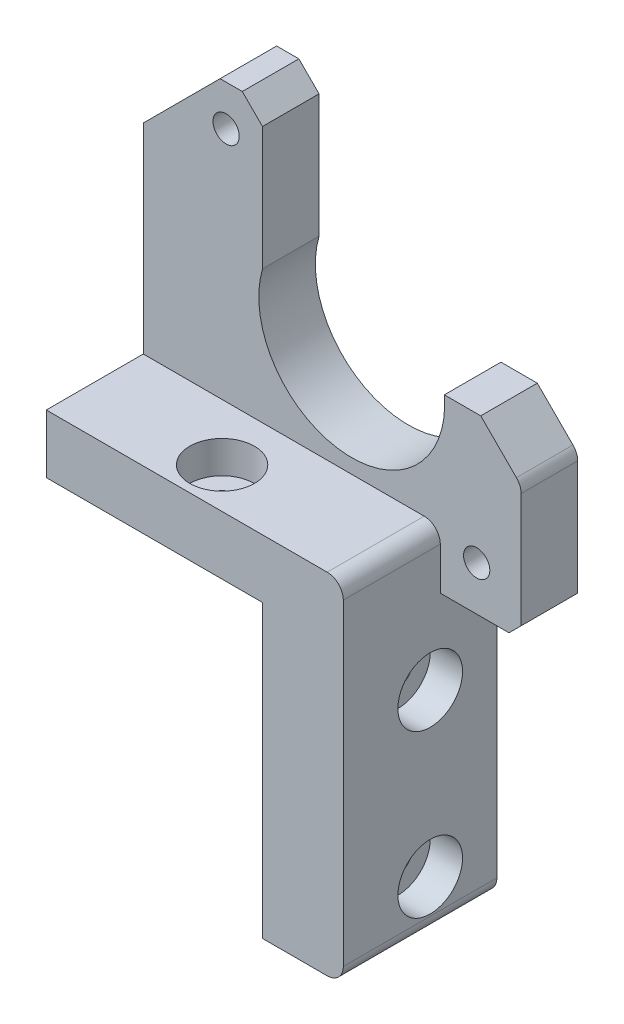
SolidWorks part; units mm, degrees
ref_plane "Front Plane" through (0, 0, 0) normal (0, 0, 1) x (1, 0, 0)
ref_plane "Top Plane" through (0, 0, 0) normal (0, 1, 0) x (1, 0, 0)
ref_plane "Right Plane" through (0, 0, 0) normal (1, 0, 0) x (0, 0, -1)
sketch "Sketch1" plane through (0, 0, 0) normal (0, 0, 1) x (1, 0, 0)
  line L0 (0, 0) -> (10, 0)
  line L1 (10, 0) -> (10, 43.25)
  line L2 (10, 43.25) -> (-26.75, 43.25)
  line L3 (-26.75, 43.25) -> (-26.75, 36)
  line L4 (-26.75, 36) -> (0, 36)
  line L5 (0, 36) -> (0, 0)
  dimension "D1" = 10
  dimension "D2" = 43.25
  dimension "D3" = 26.75
  dimension "D4" = 36
extrude "Boss-Extrude1" add sketch "Sketch1" along normal blind 19
sketch "Sketch2" plane through (0, 0, 0) normal (0, 0, -1) x (-1, 0, 0)
  line L0 (-10, 36) -> (26.75, 36)
  line L1 (26.75, 36) -> (26.75, 68)
  line L2 (26.75, 68) -> (17.25, 77.5)
  line L3 (17.25, 77.5) -> (14.5, 77.5)
  line L4 (14.5, 77.5) -> (12, 75)
  line L5 (12, 75) -> (12, 59.75)
  line L7 (-10, 0) -> (-10, 43.25) construction
  line L8 (-10, 36) -> (-18.5, 36)
  line L9 (-18.5, 36) -> (-20, 37.5)
  line L10 (-20, 37.5) -> (-20, 52.5)
  line L11 (-20, 52.5) -> (-15, 57.5)
  line L12 (-15, 57.5) -> (-10.5, 57.5)
  arc A0 (-10.5, 57.5) -> (12, 59.75) centre (0.9592, 56.5326) ccw
  dimension "D16" = 23
  dimension "D1" = 45
  dimension "D2" = 32
  dimension "D3" = 9.5
  dimension "D4" = 2.75
  dimension "D5" = 45
  dimension "D6" = 2.5
  dimension "D7" = 15.25
  dimension "D9" = 8.5
  dimension "D10" = 135
  dimension "D11" = 1.5
  dimension "D12" = 15
  dimension "D13" = 45
  dimension "D14" = 5
  dimension "D15" = 4.5
extrude "Boss-Extrude2" add sketch "Sketch2" against normal blind 7
sketch "Sketch3" plane through (10, 0, 0) normal (1, 0, 0) x (0, 0, -1)
  line L0 (0, 0) -> (0, 36) construction
  line L1 (-8.25, 26.25) -> (-8.25, 6.25) construction
  line L2 (-19, 0) -> (0, 0) construction
  circle A0 centre (-8.25, 26.25) radius 1.75
  circle A1 centre (-8.25, 6.25) radius 1.75
  dimension "D4" = 3.5
  dimension "D1" = 8.25
  dimension "D2" = 26.25
  dimension "D3" = 6.25
extrude "Cut-Extrude1" cut sketch "Sketch3" against normal through all
sketch "Sketch6" plane through (10, 0, 0) normal (1, 0, 0) x (0, 0, -1)
  circle A0 centre (-8.25, 26.25) radius 4
  circle A1 centre (-8.25, 6.25) radius 4
  dimension "D1" = 8
extrude "Cut-Extrude4" cut sketch "Sketch6" against normal blind 4
sketch "Sketch7" plane through (0, 0, 0) normal (0, 0, -1) x (-1, 0, 0)
  line L0 (-18.5, 36) -> (-10, 36) construction
  line L1 (-20, 52.5) -> (-20, 37.5) construction
  line L2 (26.75, 36) -> (0, 36) construction
  circle A0 centre (16.5, 72.5) radius 1.625
  circle A1 centre (-14.5, 41.5) radius 1.625
  dimension "D1" = 3.25
  dimension "D2" = 3.25
  dimension "D3" = 5.5
  dimension "D4" = 5.5
  dimension "D5" = 36.5
  dimension "D6" = 36.5
extrude "Cut-Extrude5" cut sketch "Sketch7" against normal through all
fillet "Fillet1" radius 2 3 edges at (10, 43.25, 13) (20, 52.5, 3.5) (10, 0, 9.5)
sketch "Sketch8" plane through (0, 36, 0) normal (0, -1, 0) x (1, 0, 0)
  line L0 (0, 19) -> (0, 0) construction
  line L1 (-26.75, 0) -> (0, 0) construction
  line L2 (-26.75, 19) -> (0, 19) construction
  circle A0 centre (-10, 14) radius 1.75
  dimension "D1" = 10
  dimension "D2" = 14
extrude "Cut-Extrude6" cut sketch "Sketch8" against normal blind 10
sketch "Sketch9" plane through (0, 43.25, 0) normal (0, 1, 0) x (1, 0, 0)
  circle A0 centre (-10, -14) radius 4
extrude "Cut-Extrude7" cut sketch "Sketch9" against normal blind 4
